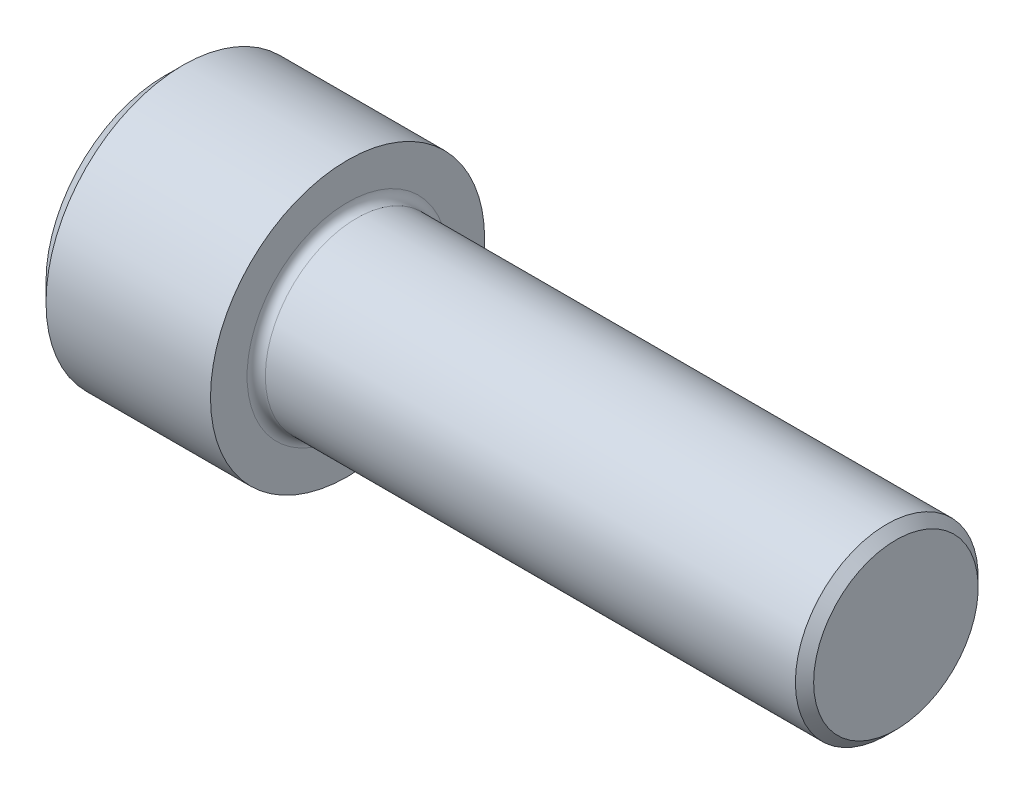
SolidWorks part; units mm, degrees
ref_plane "Plane1" through (0, 0, 0) normal (0, 0, 1) x (1, 0, 0)
ref_plane "Plane2" through (0, 0, 0) normal (0, 1, 0) x (1, 0, 0)
ref_plane "Plane3" through (0, 0, 0) normal (1, 0, 0) x (0, 0, -1)
sketch "BodySke" plane through (0, 0, 0) normal (0, 0, 1) x (1, 0, 0)
  line L0 (0, 0) -> (0, 16.51)
  line L1 (2.54, 19.05) -> (25.4, 19.05)
  line L2 (25.4, 19.05) -> (25.4, 12.7)
  line L3 (25.4, 12.7) -> (100.3313, 12.7)
  line L4 (101.6, 11.4313) -> (101.6, 0)
  line L5 (101.6, 0) -> (0, 0)
  line L6 (-31.75, 0) -> (127, 0) construction
  line L7 (0, 16.51) -> (2.54, 19.05)
  line L8 (101.6, 11.4313) -> (100.3313, 12.7)
  line L9 (0, -16.51) -> (2.54, -19.05) construction
  line L10 (101.6, -11.4313) -> (100.3313, -12.7) construction
  line L11 (27.5167, 9.525) -> (27.5167, 3.175) construction
  line L12 (63.5, 9.525) -> (63.5, 3.175) construction
  line L13 (63.5, 9.525) -> (63.5, 3.175) construction
  dimension "Diameter" = 25.4
  dimension "Head_ht" = 25.4
  dimension "Length" = 76.2
  dimension "Body_ch_ang" = 45
  dimension "Head_dia" = 38.1
  dimension "Head_ch_ang" = 45
  dimension "Head_side_ht" = 22.86
  dimension "Minor_dia" = 22.8625
  dimension "Advance" = 2.1167
  dimension "Thread_nom" = 38.1
  dimension "Thread_length" = 38.1
revolve "Base-Revolve" add sketch "BodySke"
cosmetic thread "ThreadCosmetic" [suppressed]
fillet "Fillet1" radius 1.27 1 edges at (25.4, 0, 12.7)
sketch "Sketch2" plane through (0, 0, 0) normal (0, 0, 1) x (1, 0, 0)
  line L0 (0, 9.525) -> (12.573, 9.525)
  line L1 (12.573, 9.525) -> (18.0723, 0)
  line L2 (-31.75, 0) -> (127, 0) construction
  line L3 (18.0723, 0) -> (0, 0)
  line L4 (0, 0) -> (0, 9.525)
  line L5 (0, 16.51) -> (0, -16.51) construction
  line L6 (0, 0) -> (47.625, 0) construction
  line L7 (25.4, -19.05) -> (25.4, 19.05) construction
  dimension "D1" = 9.525
  dimension "D2" = 60
  dimension "Wall_thickness" = 12.827
revolve "Hex-PreBroach" cut sketch "Sketch2" angle 360 about L6
sketch "Sketch3" plane through (0, 0, 0) normal (-1, 0, 0) x (0, 0.5, 0.866)
  line L0 (5.4993, 9.525) -> (-5.4993, 9.525)
  line L1 (-5.4993, 9.525) -> (-10.9985, 0)
  line L2 (5.4993, 9.525) -> (10.9985, 0)
  line L3 (5.4993, -9.525) -> (10.9985, 0)
  line L4 (5.4993, -9.525) -> (-5.4993, -9.525)
  line L5 (-5.4993, -9.525) -> (-10.9985, 0)
  dimension "D1" = 9.525
  dimension "D2" = 9.525
  dimension "Hex_size" = 19.05
extrude "Hex" cut sketch "Sketch3" against normal blind 12.573
sketch "Sketch4" plane through (0, 0, 0) normal (-1, 0, 0) x (0, 0, 1)
  line L0 (0, 0) -> (10.1727, 0)
  line L1 (0, 0) -> (6.1484, 3.5498) construction
  line L2 (0, 0) -> (5.0863, 8.8098)
  line L3 (8.4417, 2.1022) -> (9.7612, 2.864)
  line L4 (6.0414, 6.2596) -> (7.3609, 7.0215)
  arc A0 (8.4417, 2.1022) -> (6.0414, 6.2596) centre (0, 0) ccw
  arc A1 (10.1727, 0) -> (9.7612, 2.864) centre (0, 0) ccw
  arc A2 (5.0863, 8.8098) -> (7.3609, 7.0215) centre (0, 0) cw
  dimension "D1" = 30
  dimension "Spline_n_dim" = 17.399
  dimension "Spline_m_dim" = 20.3454
  dimension "D2" = 60
  dimension "D3" = 2.4003
  dimension "Spline_p_dim" = 4.8006
extrude "Spline" [suppressed] cut sketch "Sketch4" against normal blind 12.573
pattern_circular "CirPattern1" [suppressed] count 6 every 60
sketch "Sketch5" plane through (0, 0, 0) normal (0, 0, 1) x (1, 0, 0)
  line L0 (-31.75, 0) -> (127, 0) construction
  line L2 (0, 16.51) -> (0, -16.51) construction
  circle A0 centre (7.874, 0) radius 1.1874
  dimension "Drilled_hole_dia" = 2.3749
  dimension "Drilled_hole_loc" = 7.874
extrude "Hole" [suppressed] cut sketch "Sketch5" against normal through all and the other way through all
pattern_circular "Drilled-4" [suppressed] count 2 every 60
pattern_circular "Drilled-6" [suppressed] count 3 every 60
sketch "ThdSchSke" plane through (0, 0, 0) normal (0, 0, 1) x (1, 0, 0)
  line L0 (63.5, -11.4313) -> (62.6116, -12.7)
  line L1 (63.5, -11.4313) -> (64.3884, -12.7)
  line L2 (64.3884, -12.7) -> (64.3884, -15.875)
  line L3 (-3.175, 0) -> (5.1513, 0) construction
  line L5 (64.3884, -15.875) -> (62.6116, -15.875)
  line L6 (62.6116, -15.875) -> (62.6116, -12.7)
  line L7 (0, 16.51) -> (0, -16.51) construction
  dimension "Thread_minor" = 22.8625
  dimension "Diameter" = 25.4
  dimension "Start" = 63.5
  dimension "SideAngle" = 55
  dimension "VeeAngle" = 70
  dimension "Overcut" = 31.75
revolve "ThreadSchematic" [suppressed] cut sketch "ThdSchSke" angle 360 about L3
pattern_linear "ThdSchPat" [suppressed]
equation "\"D2@Sketch3\" = \"Hex_size@Sketch3\" / 2"
equation "\"D1@Sketch3\" = \"Hex_size@Sketch3\" / 2"
equation "\"D1@Sketch2\" = \"Hex_size@Sketch3\" / 2"
equation "\"D3@Sketch4\" = \"Spline_p_dim@Sketch4\" / 2"
equation "\"Thread_minor@ThreadCosmetic\"  =  \"Minor_dia@BodySke\""
equation "\"D2@CirPattern1\" = 360 / \"Num_teeth@CirPattern1\""
equation "\"Wall_thickness@Sketch2\" = \"Head_ht@BodySke\" - \"Key_eng@Hex\""
equation "\"Thread_length@ThreadCosmetic\" = ((sgn( (\"Length@BodySke\" - \"Advance@BodySke\" ) - \"Thread_nom@BodySke\" )-1)*( (\"Length@BodySke\" - \"Advance@BodySke\" ) - \"Thread_nom@BodySke\" ))/-2+ \"Thread_nom@BodySke\""
equation "\"Thread_minor@ThdSchSke\" = \"Minor_dia@BodySke\""
equation "\"Diameter@ThdSchSke\" = \"Diameter@BodySke\""
equation "\"Overcut@ThdSchSke\" = \"Diameter@BodySke\" * 1.25"
equation "\"Start@ThdSchSke\" = \"Head_ht@BodySke\" + \"Length@BodySke\" - \"Thread_length@ThreadCosmetic\"  '---Non-countersunk---"
equation "\"Num_threads@ThdSchPat\" = int( \"Thread_length@ThreadCosmetic\" / \"Advance@BodySke\" + 0.999 )  + 1"
equation "\"Advance@ThdSchPat\" = \"Thread_length@ThreadCosmetic\" /  (\"Num_threads@ThdSchPat\" - 1) 'relax it"
equation "\"Num_threads@ThdSchPat\" = \"Num_threads@ThdSchPat\" - sgn( \"Num_threads@ThdSchPat\" - 1) '---chamfered tips only---"
